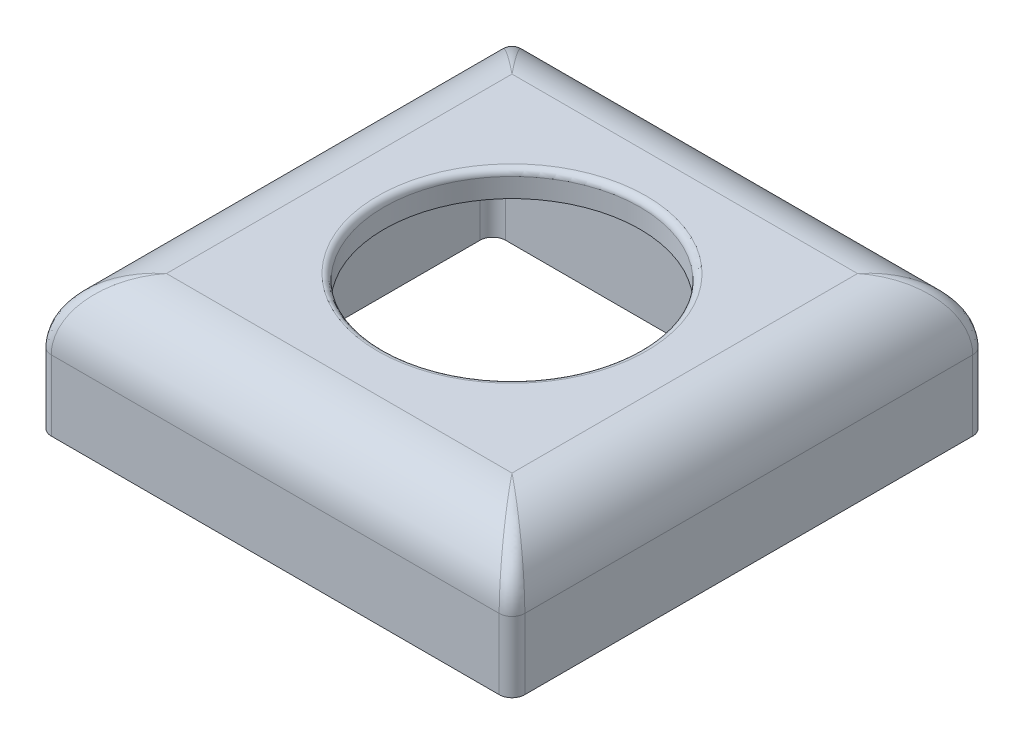
SolidWorks part; units mm, degrees
ref_plane "前视基准面" through (0, 0, 0) normal (0, 0, 1) x (1, 0, 0)
ref_plane "上视基准面" through (0, 0, 0) normal (0, 1, 0) x (1, 0, 0)
ref_plane "右视基准面" through (0, 0, 0) normal (1, 0, 0) x (0, 0, -1)
sketch "草图1" plane through (0, 0, 0) normal (0, 1, 0) x (1, 0, 0)
  line L1 (-18.5, 18.5) -> (18.5, 18.5)
  line L2 (-18.5, 18.5) -> (-18.5, -18.5)
  line L3 (-18.5, -18.5) -> (18.5, -18.5)
  line L4 (18.5, 18.5) -> (18.5, -18.5)
  line L5 (-18.5, 18.5) -> (18.5, -18.5) construction
  line L6 (-18.5, -18.5) -> (18.5, 18.5) construction
  point P0 (0, 0)
  dimension "D1" = 37
  dimension "D2" = 37
extrude "凸台-拉伸1" add sketch "草图1" along normal blind 10.5
sketch "草图2" plane through (0, 0, 0) normal (0, -1, 0) x (1, 0, 0)
  circle A0 centre (0, 0) radius 10
  dimension "D1" = 20
extrude "切除-拉伸1" cut sketch "草图2" against normal through all
fillet "圆角1" radius 5 4 edges at (18.5, 10.5, 0) (0, 10.5, 18.5) (-18.5, 10.5, 0) (0, 10.5, -18.5)
fillet "圆角2" radius 1 8 edges at (-17.0355, 9.0355, -17.0355) (17.0355, 9.0355, -17.0355) (17.0355, 9.0355, 17.0355) (-17.0355, 9.0355, 17.0355) (-18.5, 2.75, -18.5) (18.5, 2.75, -18.5) (18.5, 2.75, 18.5) (-18.5, 2.75, 18.5)
sketch "草图3" plane through (0, 0, 0) normal (0, -1, 0) x (1, 0, 0)
  line L0 (17.5, -18.5) -> (-17.5, -18.5) construction
  line L1 (-18.5, -17.5) -> (-18.5, 17.5) construction
  line L2 (-17.5, 18.5) -> (17.5, 18.5) construction
  line L3 (18.5, 17.5) -> (18.5, -17.5) construction
  circle A0 centre (15, 15) radius 1.5
  circle A2 centre (15, -15) radius 1.5
  circle A3 centre (0, -15) radius 1.5
  circle A4 centre (-15, -15) radius 1.5
  circle A6 centre (-15, 15) radius 1.5
  circle A7 centre (0, 15) radius 1.5
  dimension "D1" = 3
  dimension "D3" = 3
  dimension "D4" = 3
  dimension "D5" = 3
  dimension "D7" = 3
  dimension "D8" = 3
  dimension "D11" = 0
  dimension "D12" = 0
  dimension "D13" = 3.5
  dimension "D16" = 3.5
  dimension "D18" = 3.5
  dimension "D19" = 3.5
  dimension "D20" = 3.5
  dimension "D21" = 3.5
  dimension "D22" = 3.5
  dimension "D24" = 3.5
  dimension "D14" = 3.5
  dimension "D15" = 3.5
extrude "切除-拉伸2" cut sketch "草图3" against normal blind 4
sketch "草图4" plane through (0, 0, 0) normal (0, -1, 0) x (1, 0, 0)
  line L1 (13, 12.5) -> (-13, 12.5)
  line L2 (14, 11.5) -> (14, -11.5)
  line L3 (13, -12.5) -> (-13, -12.5)
  line L4 (-14, 11.5) -> (-14, -11.5)
  line L5 (14, 12.5) -> (-14, -12.5) construction
  line L6 (14, -12.5) -> (-14, 12.5) construction
  arc A0 (14, 11.5) -> (13, 12.5) centre (13, 11.5) ccw
  arc A1 (-14, 11.5) -> (-13, 12.5) centre (-13, 11.5) cw
  arc A2 (-14, -11.5) -> (-13, -12.5) centre (-13, -11.5) ccw
  arc A3 (13, -12.5) -> (14, -11.5) centre (13, -11.5) ccw
  point P0 (0, 0)
  dimension "D3" = 1
  dimension "D1" = 25
  dimension "D2" = 28
extrude "切除-拉伸3" cut sketch "草图4" against normal blind 8.5
sketch "草图5" plane through (0, 0, 0) normal (0, -1, 0) x (1, 0, 0)
  line L12 (-17, 17) -> (-17, -17)
  line L13 (-17, -17) -> (17, -17)
  line L14 (17, -17) -> (17, 17)
  line L15 (17, 17) -> (-17, 17)
  line L16 (-17, 12.1277) -> (-17, -12.1277)
  line L17 (-12.1277, -17) -> (-2.8723, -17)
  line L18 (17, -12.1277) -> (17, 12.1277)
  line L19 (12.1277, 17) -> (2.8723, 17)
  line L33 (-3.3541, 14) -> (-11.6459, 14)
  line L34 (-2.8723, 17) -> (-12.1277, 17)
  line L35 (2.8723, -17) -> (12.1277, -17)
  line L36 (3.3541, -14) -> (11.6459, -14)
  line L37 (15.5, -11.5) -> (15.5, 11.5)
  line L38 (13, 14) -> (-13, 14)
  line L39 (-15.5, 11.5) -> (-15.5, -11.5)
  line L40 (-13, -14) -> (13, -14)
  line L41 (15.5, -11.5359) -> (15.5, 11.5359)
  line L42 (11.6459, 14) -> (3.3541, 14)
  line L43 (-15.5, 11.5359) -> (-15.5, -11.5359)
  line L44 (-11.6459, -14) -> (-3.3541, -14)
  circle A2 centre (15, 15) radius 3.5
  arc A3 (15.5, 11.5359) -> (17, 12.1277) centre (15, 15) ccw
  circle A5 centre (0, 15) radius 3.5
  arc A6 (3.3541, 14) -> (2.8723, 17) centre (0, 15) ccw
  circle A8 centre (-15, 15) radius 3.5
  arc A9 (-11.6459, 14) -> (-12.1277, 17) centre (-15, 15) ccw
  circle A11 centre (15, -15) radius 3.5
  arc A12 (17, -12.1277) -> (15.5, -11.5359) centre (15, -15) ccw
  circle A14 centre (0, -15) radius 3.5
  arc A15 (2.8723, -17) -> (3.3541, -14) centre (0, -15) ccw
  circle A17 centre (-15, -15) radius 3.5
  arc A18 (-15.5, -11.5359) -> (-17, -12.1277) centre (-15, -15) ccw
  arc A24 (12.1277, 17) -> (11.6459, 14) centre (15, 15) ccw
  arc A25 (-2.8723, 17) -> (-3.3541, 14) centre (0, 15) ccw
  arc A26 (-17, 12.1277) -> (-15.5, 11.5359) centre (-15, 15) ccw
  arc A27 (-12.1277, -17) -> (-11.6459, -14) centre (-15, -15) ccw
  arc A28 (-13, 14) -> (-15.5, 11.5) centre (-13, 11.5) ccw
  arc A29 (-15.5, -11.5) -> (-13, -14) centre (-13, -11.5) ccw
  arc A30 (15.5, 11.5) -> (13, 14) centre (13, 11.5) ccw
  arc A31 (13, -14) -> (15.5, -11.5) centre (13, -11.5) ccw
  arc A32 (-3.3541, -14) -> (-2.8723, -17) centre (0, -15) ccw
  arc A33 (11.6459, -14) -> (12.1277, -17) centre (15, -15) ccw
  dimension "D1" = 2
  dimension "D2" = 2
  dimension "D3" = 2
  dimension "D4" = 2
  dimension "D5" = 2
  dimension "D6" = 2
  dimension "D7" = 1.5
  dimension "D8" = 1.5
extrude "切除-拉伸4" cut sketch "草图5" against normal up to surface (8.5 mm away) up to face at (0, 8.5, 0)
fillet "圆角4" radius 0.5 1 edges at (0, 10.5, -10)
